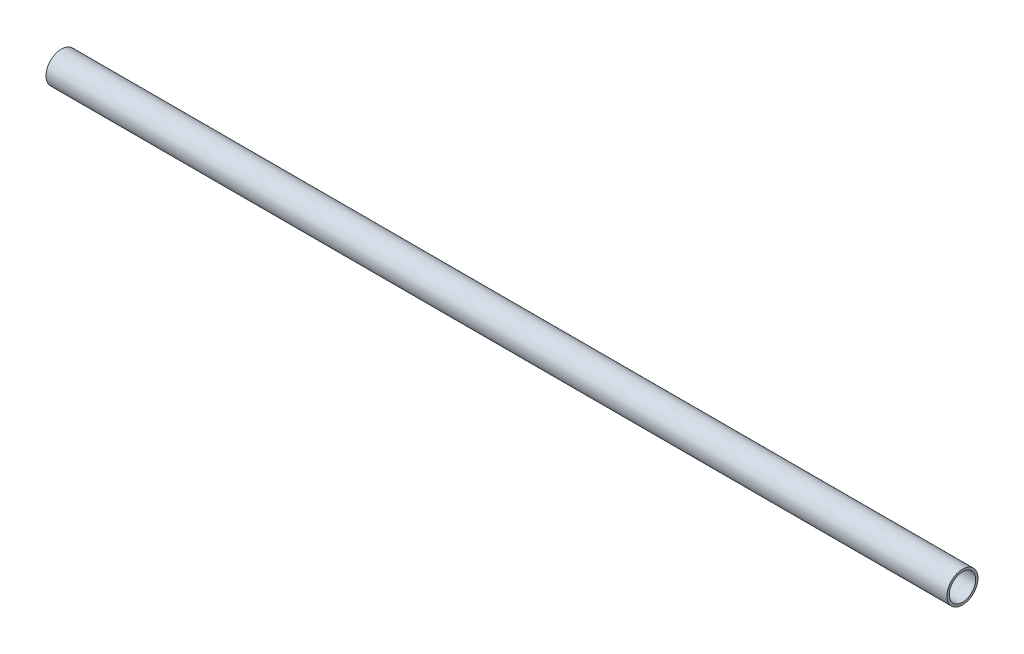
SolidWorks part; units mm, degrees
ref_plane "Front Plane" through (0, 0, 0) normal (0, 0, 1) x (1, 0, 0)
ref_plane "Top Plane" through (0, 0, 0) normal (0, 1, 0) x (1, 0, 0)
ref_plane "Right Plane" through (0, 0, 0) normal (1, 0, 0) x (0, 0, -1)
sketch "Sketch1" plane through (0, 0, 0) normal (1, 0, 0) x (0, 0, -1)
  circle A0 centre (0, 0) radius 10.795
  circle A1 centre (0, 0) radius 12.7
  dimension "D1" = 21.59
  dimension "D2" = 25.4
extrude "Boss-Extrude1" add sketch "Sketch1" along normal blind 736.6
sketch "Sketch3" plane through (0, 0, 0) normal (0, 0, 1) x (1, 0, 0)
  line L0 (0, 0) -> (50.8, 0) construction
  line L1 (50.8, 0) -> (101.6, 0) construction
  circle A0 centre (50.8, 0) radius 1.5875
  circle A1 centre (101.6, 0) radius 1.5875
  circle A2 centre (152.4, 0) radius 1.5875
  circle A3 centre (203.2, 0) radius 1.5875
  circle A4 centre (254, 0) radius 1.5875
  circle A5 centre (304.8, 0) radius 1.5875
  circle A6 centre (355.6, 0) radius 1.5875
  circle A7 centre (406.4, 0) radius 1.5875
  circle A8 centre (457.2, 0) radius 1.5875
  circle A9 centre (508, 0) radius 1.5875
  circle A10 centre (558.8, 0) radius 1.5875
  circle A11 centre (609.6, 0) radius 1.5875
  circle A12 centre (660.4, 0) radius 1.5875
  circle A13 centre (711.2, 0) radius 1.5875
  dimension "D2" = 3.175
  dimension "D1" = 50.8
  dimension "D4" = 50.8
  dimension "D3" = 14
extrude "Cut-Extrude2" cut sketch "Sketch3" against normal through all
